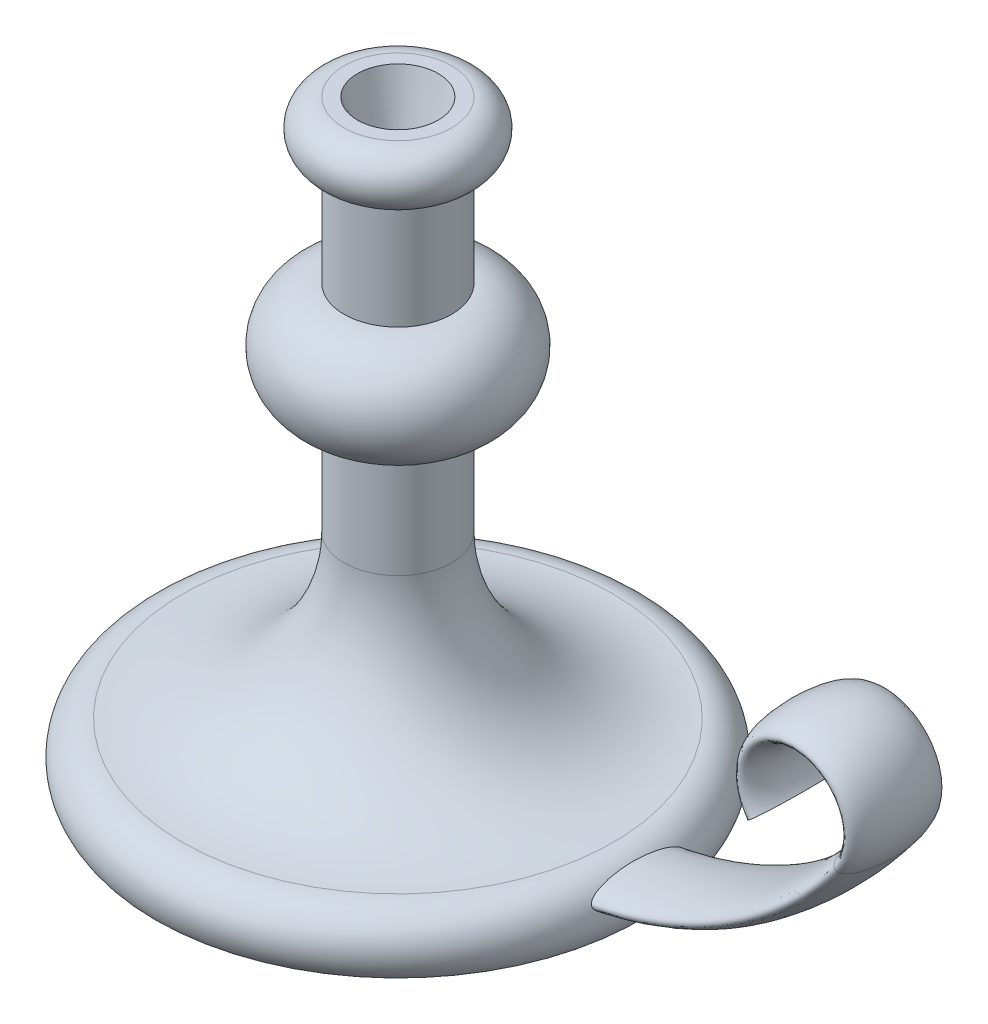
SolidWorks part; units mm, degrees
ref_plane "Płaszczyzna przednia" through (0, 0, 0) normal (0, 0, 1) x (1, 0, 0)
ref_plane "Płaszczyzna górna" through (0, 0, 0) normal (0, 1, 0) x (1, 0, 0)
ref_plane "Płaszczyzna prawa" through (0, 0, 0) normal (1, 0, 0) x (0, 0, -1)
sketch "Szkic1" plane through (0, 0, 0) normal (0, 0, 1) x (1, 0, 0)
  line L0 (0, 0) -> (0, 220)
  line L3 (0, 220) -> (20, 220)
  line L4 (20, 200) -> (20, 160)
  line L5 (20, 120) -> (20, 80)
  line L6 (0, 0) -> (90, 0)
  arc A0 (20, 220) -> (20, 200) centre (20, 210) cw
  arc A1 (20, 160) -> (20, 120) centre (20, 140) cw
  arc A2 (20, 80) -> (80, 20) centre (80, 80) ccw
  arc A3 (80, 20) -> (90, 0) centre (80, 7.5) cw
  dimension "D3" = 10
  dimension "D5" = 20
  dimension "D6" = 60
  dimension "D8" = 12.5
  dimension "D1" = 220
  dimension "D2" = 20
  dimension "D4" = 40
  dimension "D7" = 90
  dimension "D9" = 80
revolve "Obrót1" add sketch "Szkic1" angle 360 about L0
sketch "Szkic12" plane through (0, 0, 0) normal (0, 0, 1) x (1, 0, 0)
  line L0 (0, 10) -> (60, 10)
  arc A0 (60, 10) -> (180, 70) centre (60, 160) ccw
  arc A1 (180, 70) -> (148, 70) centre (164, 82) ccw
  dimension "D2" = 10
  dimension "D3" = 150
  dimension "D4" = 20
  dimension "D1" = 60
  dimension "D5" = 60
sketch "Szkic13" plane through (0, 0, 0) normal (1, 0, 0) x (0, 0, -1)
  ellipse E0 centre (0, 10) end of major axis (17.5, 10) minor radius 5
  dimension "D1" = 35
  dimension "D2" = 10
sweep "Wyciągnięcie po ścieżce1" add profiles "Szkic13" path "Szkic12"
sketch "Szkic14" plane through (0, 220, 0) normal (0, 1, 0) x (1, 0, 0)
  circle A0 centre (0, 0) radius 15
  dimension "D1" = 30
extrude "Wytnij-wyciągnięcie1" cut sketch "Szkic14" against normal blind 25 draft 15
